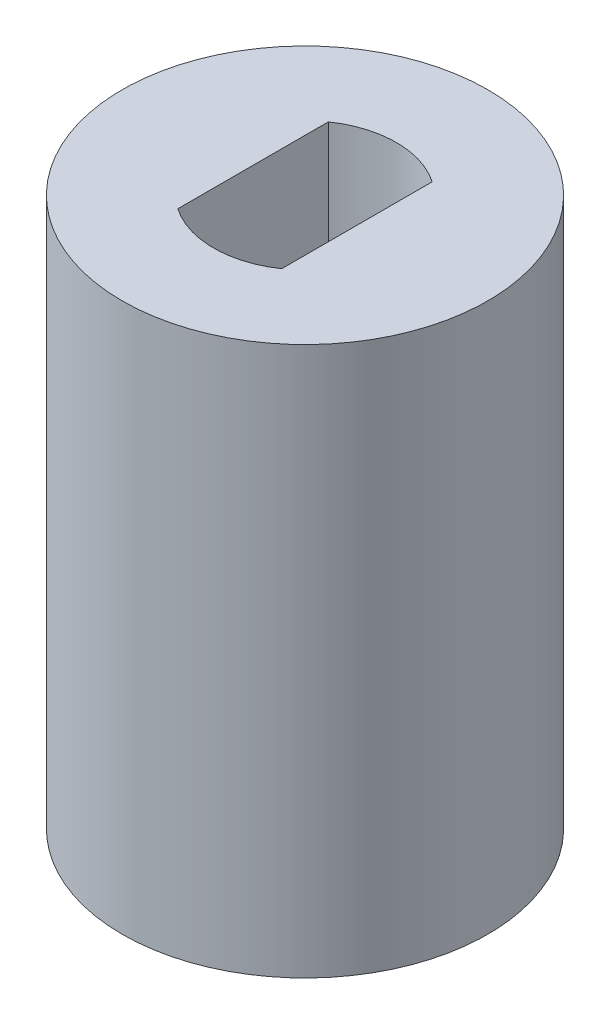
SolidWorks part; units mm, degrees
ref_plane "Front Plane" through (0, 0, 0) normal (0, 0, 1) x (1, 0, 0)
ref_plane "Top Plane" through (0, 0, 0) normal (0, 1, 0) x (1, 0, 0)
ref_plane "Right Plane" through (0, 0, 0) normal (1, 0, 0) x (0, 0, -1)
sketch "Sketch1" plane through (0, 0, 0) normal (0, 1, 0) x (1, 0, 0)
  line L0 (-1.42, 2.0576) -> (-1.42, -2.0576)
  line L1 (0, -5) -> (0, 5) construction
  line L2 (1.42, 2.0576) -> (1.42, -2.0576)
  circle A0 centre (0, 0) radius 5
  arc A1 (-1.42, -2.0576) -> (1.42, -2.0576) centre (0, 0) ccw
  arc A2 (1.42, 2.0576) -> (-1.42, 2.0576) centre (0, 0) ccw
  point P9 (0, 0)
  dimension "D1" = 5
  dimension "D3" = 10
  dimension "D2" = 1.42
extrude "Boss-Extrude1" add sketch "Sketch1" along normal blind 15 contours A0 | L0 A1 L2 A2
